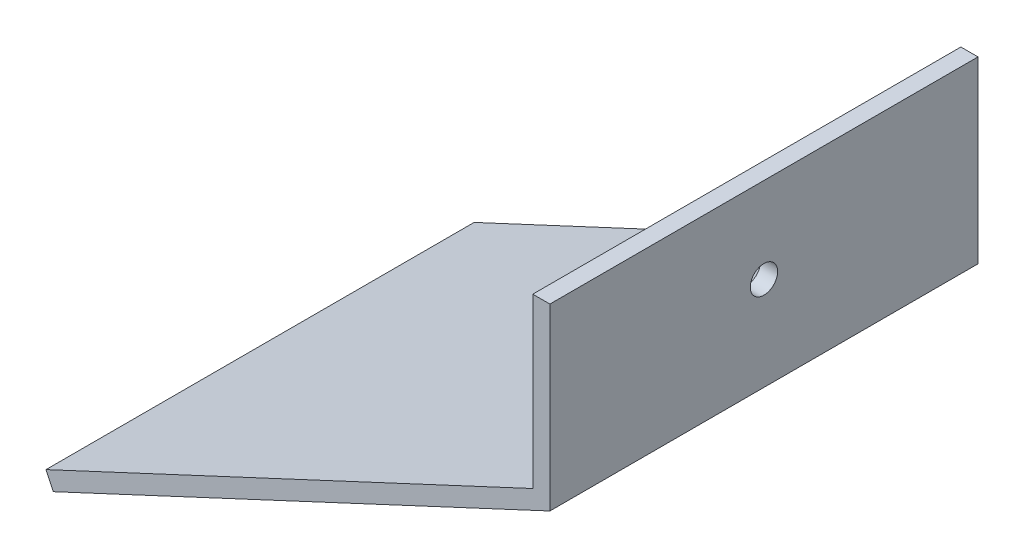
SolidWorks part; units mm, degrees
ref_plane "正面" through (0, 0, 0) normal (0, 0, 1) x (1, 0, 0)
ref_plane "平面" through (0, 0, 0) normal (0, 1, 0) x (1, 0, 0)
ref_plane "右側面" through (0, 0, 0) normal (1, 0, 0) x (0, 0, -1)
sketch "ｽｹｯﾁ1" plane through (0, 0, 0) normal (0, 0, 1) x (1, 0, 0)
  line L0 (0, 0) -> (56.8489, 26.5091)
  line L1 (56.8489, 26.5091) -> (56.8489, 46.167)
  line L2 (56.8489, 46.167) -> (58.8489, 46.167)
  line L3 (58.8489, 46.167) -> (58.8489, 25.235)
  line L4 (58.8489, 25.235) -> (0.8452, -1.8126)
  line L5 (0.8452, -1.8126) -> (0, 0)
  dimension "D1" = 64
  dimension "D2" = 2
  dimension "D3" = 2
  dimension "D4" = 115
extrude "ﾎﾞｽ - 押し出し1" add sketch "ｽｹｯﾁ1" along normal mid plane 50
sketch "ｽｹｯﾁ2" plane through (58.8489, 0, 0) normal (1, 0, 0) x (0, 0, -1)
  line L0 (0, 46.167) -> (0, 36.167)
  line L1 (-25, 46.167) -> (25, 46.167) construction
  circle A0 centre (0, 36.167) radius 1.6
  dimension "D2" = 3.2
  dimension "D1" = 10
extrude "ｶｯﾄ - 押し出し1" cut sketch "ｽｹｯﾁ2" against normal blind 50
